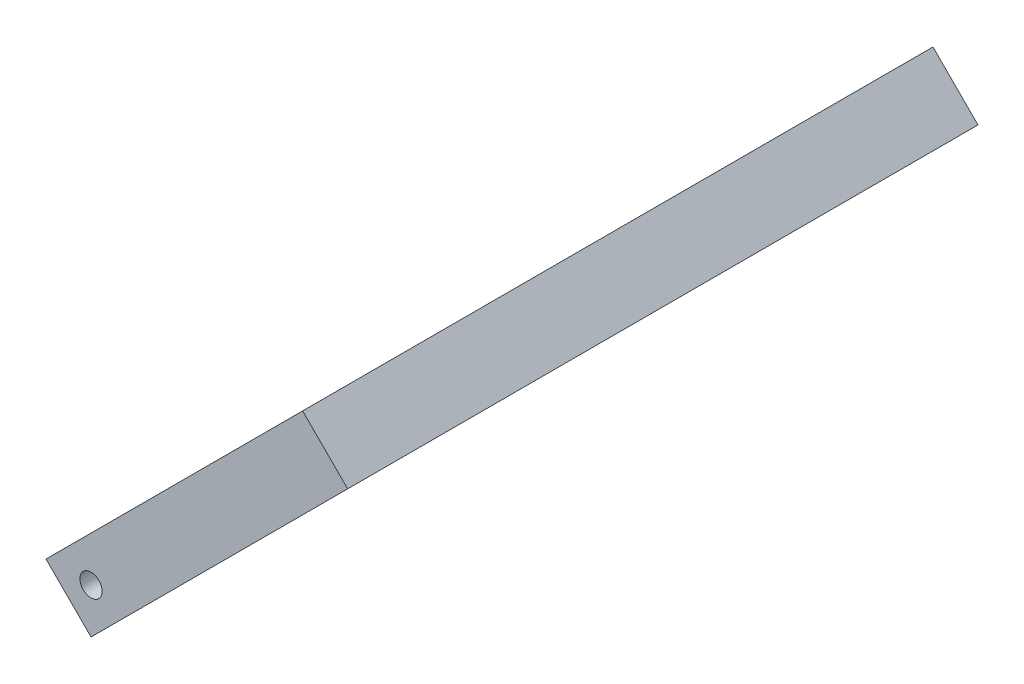
SolidWorks part; units mm, degrees
ref_plane "Front Plane" through (0, 0, 0) normal (0, 0, 1) x (1, 0, 0)
ref_plane "Top Plane" through (0, 0, 0) normal (0, 1, 0) x (1, 0, 0)
ref_plane "Right Plane" through (0, 0, 0) normal (1, 0, 0) x (0, 0, -1)
sketch "Sketch1" plane through (0, 0, 0) normal (0, 0, 1) x (1, 0, 0)
  line L0 (0, 0) -> (70.7107, 70.7107) construction
  line L1 (0, 0) -> (0, 78.4519) construction
  line L2 (67.1751, 60.1041) -> (60.1041, 67.1751)
  line L3 (60.1041, 67.1751) -> (93.3381, 100.4092)
  line L4 (93.3381, 100.4092) -> (100.4092, 93.3381)
  line L5 (100.4092, 93.3381) -> (67.1751, 60.1041)
  line L6 (96.8737, 96.8737) -> (89.8026, 89.8026) construction
  arc A0 (25.0433, 96.8134) -> (12.9, 99.1645) centre (0, 0) ccw construction
  circle A1 centre (0, 0) radius 127 construction
  point P9 (63.6396, 63.6396)
  dimension "D4" = 10
  dimension "D1" = 45
  dimension "D2" = 10
  dimension "D3" = 10
extrude "Boss-Extrude1" add sketch "Sketch1" against normal blind 5
sketch "Sketch2" plane through (96.8737, 96.8737, 0) normal (0.7071, 0.7071, 0) x (0, 0, -1)
  line L0 (69, 0) -> (99, 0) construction
  line L1 (0, -5) -> (99, -5)
  line L2 (0, -5) -> (0, 5)
  line L3 (0, 5) -> (99, 5)
  line L4 (99, -5) -> (99, 5)
  dimension "D1" = 30
extrude "Boss-Extrude2" add sketch "Sketch2" along normal blind 10
sketch "Sketch3" plane through (3.5355, -3.5355, 0) normal (0.7071, -0.7071, 0) x (0, 0, -1)
  line L0 (5, 100) -> (22.2534, 137)
  line L2 (5, 137) -> (99, 137) construction
  line L3 (22.2534, 137) -> (5, 137)
  line L4 (5, 137) -> (5, 100)
  line L12 (5, 90) -> (0, 90) construction
  dimension "D1" = 65
  dimension "D2" = 10
extrude "Boss-Extrude3" add sketch "Sketch3" against normal up to surface (10 mm away) up to face at (84.6171, 91.6882, -34.6667)
sketch "Sketch4" plane through (0, 0, 0) normal (0, 0, 1) x (1, 0, 0)
  line L0 (63.6396, 63.6396) -> (77.8845, 77.8845) construction
  line L1 (60.1041, 67.1751) -> (67.1751, 60.1041) construction
  circle A0 centre (67.1751, 67.1751) radius 1.75
  dimension "D2" = 3.5
  dimension "D1" = 5
extrude "Cut-Extrude1" cut sketch "Sketch4" against normal through all
